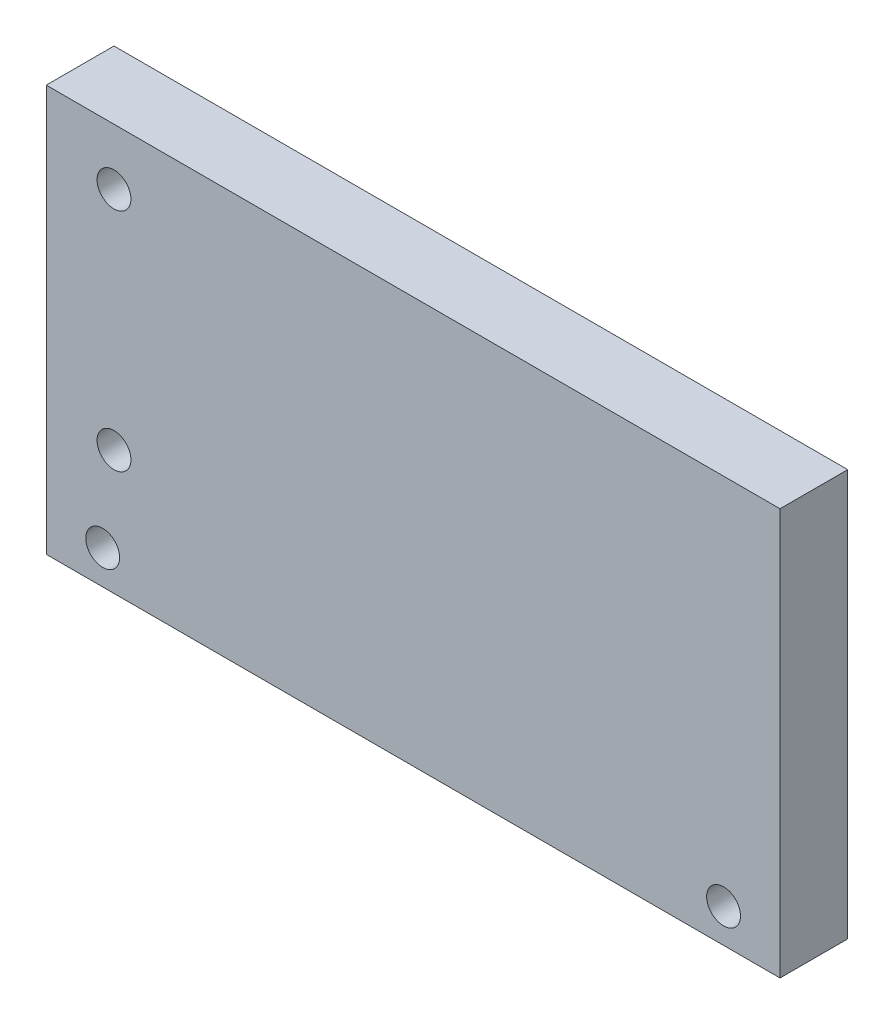
SolidWorks part; units mm, degrees
ref_plane "Plan de face" through (0, 0, 0) normal (0, 0, 1) x (1, 0, 0)
ref_plane "Plan de dessus" through (0, 0, 0) normal (0, 1, 0) x (1, 0, 0)
ref_plane "Plan de droite" through (0, 0, 0) normal (1, 0, 0) x (0, 0, -1)
sketch "Esquisse1" plane through (0, 0, 0) normal (0, 0, 1) x (1, 0, 0)
  line L1 (-40.2712, 36.6319) -> (24.7288, 36.6319)
  line L2 (-40.2712, 36.6319) -> (-40.2712, 0.6319)
  line L3 (-40.2712, 0.6319) -> (24.7288, 0.6319)
  line L4 (24.7288, 36.6319) -> (24.7288, 0.6319)
  circle A2 centre (-34.2712, 31.6319) radius 1.5
  circle A3 centre (-34.2712, 11.6319) radius 1.5
  dimension "D9" = 3
  dimension "D10" = 3
  dimension "D11" = 6
  dimension "D12" = 6
  dimension "D13" = 25
  dimension "D14" = 5
  dimension "D1" = 65
  dimension "D2" = 36
extrude "Boss.-Extru.1" add sketch "Esquisse1" along normal blind 6
sketch "Esquisse3" plane through (0, 0, 6) normal (0, 0, 1) x (1, 0, 0)
  line L0 (-40.2712, 0.6319) -> (24.7288, 0.6319) construction
  line L2 (24.7288, 0.6319) -> (24.7288, 36.6319) construction
  line L3 (-40.2712, 36.6319) -> (-40.2712, 0.6319) construction
  circle A0 centre (-35.2712, 3.6319) radius 1.5
  circle A1 centre (19.7288, 3.6319) radius 1.5
  dimension "D1" = 3
  dimension "D2" = 3
  dimension "D3" = 5
  dimension "D4" = 3
  dimension "D5" = 5
extrude "Enlèv. mat.-Extru.1" cut sketch "Esquisse3" against normal blind 10
